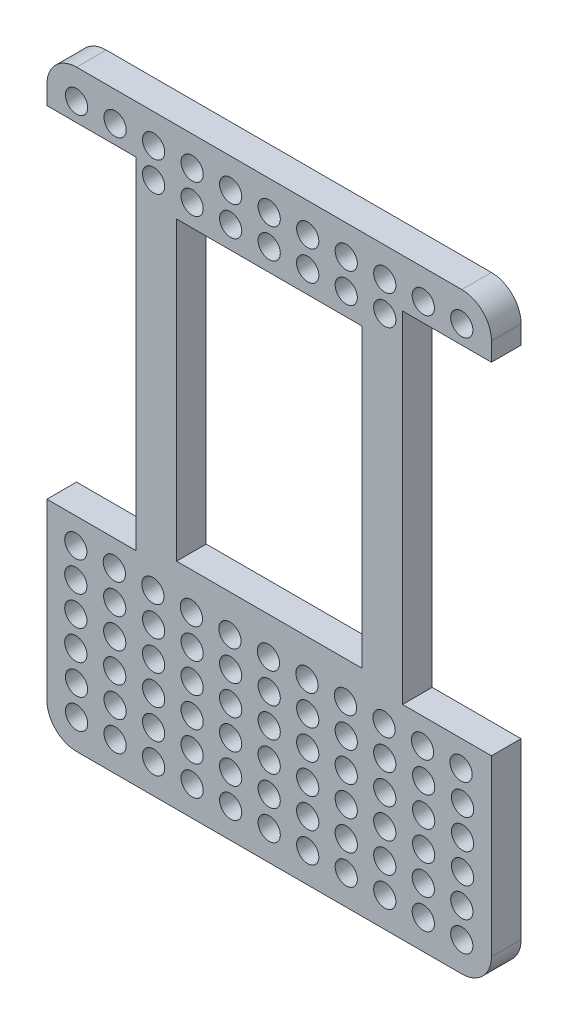
SolidWorks part; units mm, degrees
ref_plane "Спереди" through (0, 0, 0) normal (0, 0, 1) x (1, 0, 0)
ref_plane "Сверху" through (0, 0, 0) normal (0, 1, 0) x (1, 0, 0)
ref_plane "Справа" through (0, 0, 0) normal (1, 0, 0) x (0, 0, -1)
sketch "Эскиз1" plane through (0, 0, 0) normal (0, 0, 1) x (1, 0, 0)
  line L1 (4, 0) -> (56, 0)
  line L2 (0, 4) -> (0, 76)
  line L3 (4, 80) -> (56, 80)
  line L4 (60, 4) -> (60, 76)
  arc A0 (4, 0) -> (0, 4) centre (4, 4) cw
  arc A1 (56, 0) -> (60, 4) centre (56, 4) ccw
  arc A2 (56, 80) -> (60, 76) centre (56, 76) cw
  arc A3 (0, 76) -> (4, 80) centre (4, 76) cw
  point P7 (0, 0)
  point P12 (60, 80)
  point P15 (0, 80)
  dimension "D3" = 4
  dimension "D1" = 80
  dimension "D2" = 60
extrude "Бобышка-Вытянуть1" add sketch "Эскиз1" along normal blind 4 contours L2 A3 L3 A2 L4 A1 L1 A0
sketch "Эскиз3" plane through (0, 0, 4) normal (0, 0, 1) x (1, 0, 0)
  line L0 (4, 80) -> (56, 80) construction
  line L1 (0, 4) -> (0, 76) construction
  line L2 (60, 4) -> (60, 76) construction
  line L3 (30, 0) -> (30, 25.8811) construction
  line L4 (4, 0) -> (56, 0) construction
  circle A0 centre (4, 76) radius 1.5
  circle A1 centre (9.2, 76) radius 1.5
  circle A2 centre (14.4, 76) radius 1.5
  circle A3 centre (19.6, 76) radius 1.5
  circle A4 centre (24.8, 76) radius 1.5
  circle A5 centre (30, 76) radius 1.5
  circle A6 centre (35.2, 76) radius 1.5
  circle A7 centre (40.4, 76) radius 1.5
  circle A8 centre (45.6, 76) radius 1.5
  circle A9 centre (50.8, 76) radius 1.5
  circle A10 centre (56, 76) radius 1.5
  circle A13 centre (14.4, 72) radius 1.5
  circle A14 centre (19.6, 72) radius 1.5
  circle A15 centre (24.8, 72) radius 1.5
  circle A16 centre (30, 72) radius 1.5
  circle A17 centre (35.2, 72) radius 1.5
  circle A18 centre (40.4, 72) radius 1.5
  circle A19 centre (45.6, 72) radius 1.5
  circle A156 centre (14.4, 20) radius 1.5
  circle A157 centre (19.6, 20) radius 1.5
  circle A158 centre (24.8, 20) radius 1.5
  circle A159 centre (30, 20) radius 1.5
  circle A160 centre (35.2, 20) radius 1.5
  circle A161 centre (40.4, 20) radius 1.5
  circle A162 centre (45.6, 20) radius 1.5
  circle A167 centre (14.4, 16) radius 1.5
  circle A168 centre (19.6, 16) radius 1.5
  circle A169 centre (24.8, 16) radius 1.5
  circle A170 centre (30, 16) radius 1.5
  circle A171 centre (35.2, 16) radius 1.5
  circle A172 centre (40.4, 16) radius 1.5
  circle A173 centre (45.6, 16) radius 1.5
  circle A178 centre (14.4, 12) radius 1.5
  circle A179 centre (19.6, 12) radius 1.5
  circle A180 centre (24.8, 12) radius 1.5
  circle A181 centre (30, 12) radius 1.5
  circle A182 centre (35.2, 12) radius 1.5
  circle A183 centre (40.4, 12) radius 1.5
  circle A184 centre (45.6, 12) radius 1.5
  circle A187 centre (4, 8) radius 1.5
  circle A188 centre (9.2, 8) radius 1.5
  circle A189 centre (14.4, 8) radius 1.5
  circle A190 centre (19.6, 8) radius 1.5
  circle A191 centre (24.8, 8) radius 1.5
  circle A192 centre (30, 8) radius 1.5
  circle A193 centre (35.2, 8) radius 1.5
  circle A194 centre (40.4, 8) radius 1.5
  circle A195 centre (45.6, 8) radius 1.5
  circle A196 centre (50.8, 8) radius 1.5
  circle A197 centre (56, 8) radius 1.5
  circle A198 centre (4, 4) radius 1.5
  circle A199 centre (9.2, 4) radius 1.5
  circle A200 centre (14.4, 4) radius 1.5
  circle A201 centre (19.6, 4) radius 1.5
  circle A202 centre (24.8, 4) radius 1.5
  circle A203 centre (30, 4) radius 1.5
  circle A204 centre (35.2, 4) radius 1.5
  circle A205 centre (40.4, 4) radius 1.5
  circle A206 centre (45.6, 4) radius 1.5
  circle A207 centre (50.8, 4) radius 1.5
  circle A208 centre (56, 4) radius 1.5
  circle A209 centre (30, 56) radius 1.5 [skipped]
  circle A210 centre (30, 60) radius 1.5 [skipped]
  circle A211 centre (24.8, 56) radius 1.5 [skipped]
  circle A212 centre (30, 52) radius 1.5 [skipped]
  circle A213 centre (35.2, 56) radius 1.5 [skipped]
  circle A214 centre (35.2, 60) radius 1.5 [skipped]
  circle A215 centre (24.8, 64) radius 1.5 [skipped]
  circle A216 centre (30, 64) radius 1.5 [skipped]
  circle A217 centre (35.2, 64) radius 1.5 [skipped]
  circle A218 centre (40.4, 64) radius 1.5 [skipped]
  circle A219 centre (40.4, 60) radius 1.5 [skipped]
  circle A220 centre (40.4, 56) radius 1.5 [skipped]
  circle A221 centre (40.4, 52) radius 1.5 [skipped]
  circle A222 centre (40.4, 48) radius 1.5 [skipped]
  circle A223 centre (35.2, 48) radius 1.5 [skipped]
  circle A224 centre (30, 48) radius 1.5 [skipped]
  circle A225 centre (24.8, 48) radius 1.5 [skipped]
  circle A226 centre (19.6, 48) radius 1.5 [skipped]
  circle A227 centre (19.6, 52) radius 1.5 [skipped]
  circle A228 centre (24.8, 52) radius 1.5 [skipped]
  circle A229 centre (19.6, 56) radius 1.5 [skipped]
  circle A230 centre (19.6, 60) radius 1.5 [skipped]
  circle A231 centre (24.8, 60) radius 1.5 [skipped]
  circle A232 centre (19.6, 64) radius 1.5 [skipped]
  circle A233 centre (35.2, 52) radius 1.5 [skipped]
  circle A234 centre (40.4, 44) radius 1.5 [skipped]
  circle A235 centre (35.2, 44) radius 1.5 [skipped]
  circle A236 centre (30, 44) radius 1.5 [skipped]
  circle A237 centre (24.8, 44) radius 1.5 [skipped]
  circle A238 centre (19.6, 44) radius 1.5 [skipped]
  circle A239 centre (14.4, 48) radius 1.5 [skipped]
  circle A240 centre (14.4, 52) radius 1.5 [skipped]
  circle A241 centre (14.4, 56) radius 1.5 [skipped]
  circle A242 centre (14.4, 60) radius 1.5 [skipped]
  circle A243 centre (45.6, 64) radius 1.5 [skipped]
  circle A244 centre (45.6, 60) radius 1.5 [skipped]
  circle A245 centre (45.6, 56) radius 1.5 [skipped]
  circle A246 centre (45.6, 52) radius 1.5 [skipped]
  circle A247 centre (45.6, 48) radius 1.5 [skipped]
  circle A248 centre (45.6, 44) radius 1.5 [skipped]
  circle A249 centre (14.4, 44) radius 1.5 [skipped]
  circle A250 centre (14.4, 64) radius 1.5 [skipped]
  circle A251 centre (9.2, 68) radius 1.5 [skipped]
  circle A252 centre (14.4, 68) radius 1.5 [skipped]
  circle A253 centre (19.6, 68) radius 1.5 [skipped]
  circle A254 centre (24.8, 68) radius 1.5 [skipped]
  circle A255 centre (30, 68) radius 1.5 [skipped]
  circle A256 centre (35.2, 68) radius 1.5 [skipped]
  circle A257 centre (40.4, 68) radius 1.5 [skipped]
  circle A258 centre (45.6, 68) radius 1.5 [skipped]
  circle A259 centre (50.8, 64) radius 1.5 [skipped]
  circle A260 centre (50.8, 68) radius 1.5 [skipped]
  circle A261 centre (50.8, 60) radius 1.5 [skipped]
  circle A262 centre (50.8, 56) radius 1.5 [skipped]
  circle A263 centre (50.8, 52) radius 1.5 [skipped]
  circle A264 centre (50.8, 48) radius 1.5 [skipped]
  circle A265 centre (50.8, 44) radius 1.5 [skipped]
  circle A266 centre (50.8, 40) radius 1.5 [skipped]
  circle A267 centre (50.8, 36) radius 1.5 [skipped]
  circle A268 centre (50.8, 32) radius 1.5 [skipped]
  circle A269 centre (50.8, 28) radius 1.5 [skipped]
  circle A270 centre (45.6, 28) radius 1.5 [skipped]
  circle A271 centre (45.6, 32) radius 1.5 [skipped]
  circle A272 centre (45.6, 36) radius 1.5 [skipped]
  circle A273 centre (45.6, 40) radius 1.5 [skipped]
  circle A274 centre (40.4, 40) radius 1.5 [skipped]
  circle A275 centre (35.2, 40) radius 1.5 [skipped]
  circle A276 centre (30, 40) radius 1.5 [skipped]
  circle A277 centre (24.8, 40) radius 1.5 [skipped]
  circle A278 centre (19.6, 40) radius 1.5 [skipped]
  circle A279 centre (14.4, 40) radius 1.5 [skipped]
  circle A280 centre (9.2, 40) radius 1.5 [skipped]
  circle A281 centre (4, 40) radius 1.5 [skipped]
  circle A282 centre (4, 44) radius 1.5 [skipped]
  circle A283 centre (4, 48) radius 1.5 [skipped]
  circle A284 centre (4, 52) radius 1.5 [skipped]
  circle A285 centre (4, 56) radius 1.5 [skipped]
  circle A286 centre (4, 60) radius 1.5 [skipped]
  circle A287 centre (4, 64) radius 1.5 [skipped]
  circle A288 centre (4, 68) radius 1.5 [skipped]
  circle A289 centre (9.2, 64) radius 1.5 [skipped]
  circle A290 centre (9.2, 60) radius 1.5 [skipped]
  circle A291 centre (9.2, 56) radius 1.5 [skipped]
  circle A292 centre (9.2, 52) radius 1.5 [skipped]
  circle A293 centre (9.2, 48) radius 1.5 [skipped]
  circle A294 centre (9.2, 44) radius 1.5 [skipped]
  circle A295 centre (4, 36) radius 1.5 [skipped]
  circle A296 centre (4, 32) radius 1.5 [skipped]
  circle A297 centre (4, 28) radius 1.5 [skipped]
  circle A298 centre (9.2, 24) radius 1.5 [skipped]
  circle A299 centre (4, 24) radius 1.5 [skipped]
  circle A300 centre (14.4, 24) radius 1.5 [skipped]
  circle A301 centre (19.6, 24) radius 1.5 [skipped]
  circle A302 centre (24.8, 24) radius 1.5 [skipped]
  circle A303 centre (30, 24) radius 1.5 [skipped]
  circle A304 centre (35.2, 24) radius 1.5 [skipped]
  circle A305 centre (40.4, 24) radius 1.5 [skipped]
  circle A306 centre (45.6, 24) radius 1.5 [skipped]
  circle A307 centre (50.8, 24) radius 1.5 [skipped]
  circle A308 centre (56, 24) radius 1.5 [skipped]
  circle A309 centre (56, 28) radius 1.5 [skipped]
  circle A310 centre (56, 32) radius 1.5 [skipped]
  circle A311 centre (56, 36) radius 1.5 [skipped]
  circle A312 centre (56, 40) radius 1.5 [skipped]
  circle A313 centre (56, 44) radius 1.5 [skipped]
  circle A314 centre (56, 48) radius 1.5 [skipped]
  circle A315 centre (56, 52) radius 1.5 [skipped]
  circle A316 centre (56, 56) radius 1.5 [skipped]
  circle A317 centre (56, 60) radius 1.5 [skipped]
  circle A318 centre (56, 64) radius 1.5 [skipped]
  circle A319 centre (56, 68) radius 1.5 [skipped]
  circle A320 centre (35.2, 36) radius 1.5 [skipped]
  circle A321 centre (35.2, 32) radius 1.5 [skipped]
  circle A322 centre (40.4, 28) radius 1.5 [skipped]
  circle A323 centre (40.4, 36) radius 1.5 [skipped]
  circle A324 centre (40.4, 32) radius 1.5 [skipped]
  circle A325 centre (35.2, 28) radius 1.5 [skipped]
  circle A326 centre (30, 36) radius 1.5 [skipped]
  circle A327 centre (30, 32) radius 1.5 [skipped]
  circle A328 centre (24.8, 32) radius 1.5 [skipped]
  circle A329 centre (30, 28) radius 1.5 [skipped]
  circle A330 centre (24.8, 28) radius 1.5 [skipped]
  circle A331 centre (24.8, 36) radius 1.5 [skipped]
  circle A332 centre (19.6, 36) radius 1.5 [skipped]
  circle A333 centre (14.4, 36) radius 1.5 [skipped]
  circle A334 centre (9.2, 36) radius 1.5 [skipped]
  circle A335 centre (9.2, 32) radius 1.5 [skipped]
  circle A336 centre (14.4, 32) radius 1.5 [skipped]
  circle A337 centre (19.6, 32) radius 1.5 [skipped]
  circle A338 centre (14.4, 28) radius 1.5 [skipped]
  circle A339 centre (9.2, 28) radius 1.5 [skipped]
  circle A340 centre (19.6, 28) radius 1.5 [skipped]
  circle A341 centre (9.2, 20) radius 1.5 [skipped]
  circle A342 centre (9.2, 16) radius 1.5 [skipped]
  circle A343 centre (9.2, 12) radius 1.5 [skipped]
  circle A344 centre (4, 12) radius 1.5 [skipped]
  circle A345 centre (4, 16) radius 1.5 [skipped]
  circle A346 centre (4, 20) radius 1.5 [skipped]
  circle A347 centre (50.8, 20) radius 1.5 [skipped]
  circle A348 centre (50.8, 16) radius 1.5 [skipped]
  circle A349 centre (50.8, 12) radius 1.5 [skipped]
  circle A350 centre (56, 12) radius 1.5 [skipped]
  circle A351 centre (56, 16) radius 1.5 [skipped]
  circle A352 centre (56, 20) radius 1.5 [skipped]
  circle A353 centre (50.85, 20) radius 1.5
  circle A354 centre (50.85, 16) radius 1.5
  circle A355 centre (50.85, 12) radius 1.5
  circle A356 centre (56.1, 20) radius 1.5
  circle A357 centre (56.1, 16) radius 1.5
  circle A358 centre (56.1, 12) radius 1.5
  circle A359 centre (3.9, 20) radius 1.5
  circle A360 centre (3.9, 16) radius 1.5
  circle A361 centre (3.9, 12) radius 1.5
  circle A362 centre (9.15, 12) radius 1.5
  circle A363 centre (9.15, 16) radius 1.5
  circle A364 centre (9.15, 20) radius 1.5
  circle A365 centre (3.9, 24) radius 1.5
  circle A366 centre (9.1, 24) radius 1.5
  circle A367 centre (14.3, 24) radius 1.5
  circle A368 centre (19.5, 24) radius 1.5
  circle A369 centre (24.7, 24) radius 1.5
  circle A370 centre (29.9, 24) radius 1.5
  circle A371 centre (35.1, 24) radius 1.5
  circle A372 centre (40.3, 24) radius 1.5
  circle A373 centre (45.5, 24) radius 1.5
  circle A374 centre (50.7, 24) radius 1.5
  circle A375 centre (55.9, 24) radius 1.5
  circle A376 centre (4, 72) radius 1.5 [skipped]
  circle A377 centre (9.2, 72) radius 1.5 [skipped]
  circle A378 centre (50.8, 72) radius 1.5 [skipped]
  circle A379 centre (56, 72) radius 1.5 [skipped]
  dimension "D1" = 3
  dimension "D2" = 4
  dimension "D3" = 4
  dimension "D5" = 4
  dimension "D7" = 4
  dimension "D8" = 4
  dimension "D10" = 3
  dimension "D11" = 4
  dimension "D12" = 11
  dimension "D9" = 3
  dimension "D4" = 11
  dimension "D6" = 19
extrude "Вырез-Вытянуть2" cut sketch "Эскиз3" against normal blind 4
sketch "Эскиз5" plane through (0, 0, 4) normal (0, 0, 1) x (1, 0, 0)
  line L0 (0, 4) -> (0, 76) construction
  line L1 (0, 73.5) -> (12, 73.5)
  line L2 (0, 73.5) -> (0, 27.5)
  line L3 (0, 27.5) -> (12, 27.5)
  line L4 (12, 73.5) -> (12, 27.5)
  line L5 (4, 80) -> (56, 80) construction
  line L6 (4, 0) -> (56, 0) construction
  line L7 (30, 80) -> (30, 65.7607) construction
  line L8 (60, 27.5) -> (48, 27.5)
  line L9 (48, 73.5) -> (48, 27.5)
  line L10 (60, 73.5) -> (48, 73.5)
  line L11 (60, 73.5) -> (60, 27.5)
  dimension "D1" = 12
  dimension "D2" = 46
  dimension "D3" = 6.5
  dimension "D4" = 27.5
extrude "Вырез-Вытянуть3" cut sketch "Эскиз5" against normal blind 10
sketch "Эскиз6" plane through (0, 0, 4) normal (0, 0, 1) x (1, 0, 0)
  line L0 (12, 27.5) -> (12, 73.5) construction
  line L1 (17.5, 69) -> (42.5, 69)
  line L2 (17.5, 69) -> (17.5, 29)
  line L3 (17.5, 29) -> (42.5, 29)
  line L4 (42.5, 69) -> (42.5, 29)
  line L5 (48, 73.5) -> (48, 27.5) construction
  line L6 (4, 80) -> (56, 80) construction
  dimension "D1" = 25
  dimension "D2" = 40
  dimension "D3" = 5.5
  dimension "D4" = 5.5
  dimension "D5" = 11
extrude "Вырез-Вытянуть4" cut sketch "Эскиз6" against normal blind 10
